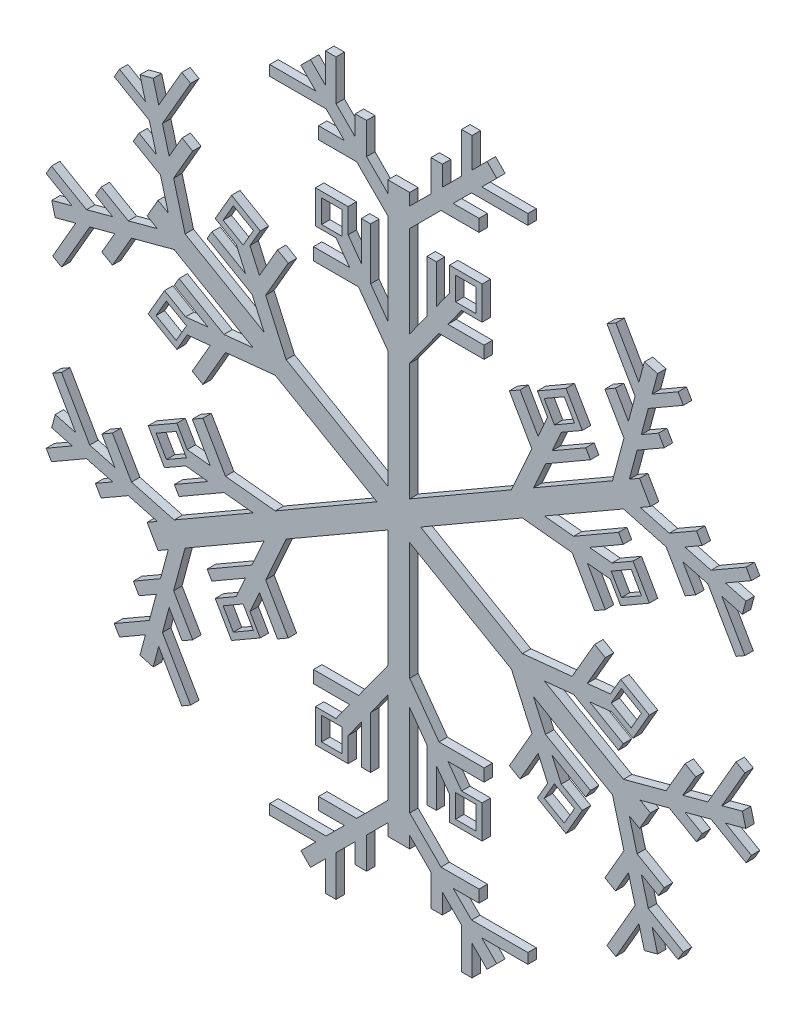
SolidWorks part; units mm, degrees
ref_plane "Front Plane" through (0, 0, 0) normal (0, 0, 1) x (1, 0, 0)
ref_plane "Top Plane" through (0, 0, 0) normal (0, 1, 0) x (1, 0, 0)
ref_plane "Right Plane" through (0, 0, 0) normal (1, 0, 0) x (0, 0, -1)
sketch "Sketch3" plane through (0, 0, 0) normal (0, 0, 1) x (1, 0, 0)
  line L0 (-3.2918, 12.5643) -> (-12.115, 24.7697)
  line L2 (-3.2918, -25.3618) -> (-3.2918, 12.5643)
  line L3 (-3.2918, 57.1281) -> (0, 57.1281)
  line L4 (0, -28.3059) -> (0, 57.1281)
  line L6 (-15.2752, 36.8018) -> (-11.2955, 31.2966)
  line L7 (-11.2955, 31.2966) -> (-11.2955, 43.0417)
  line L8 (-11.2955, 43.0417) -> (-8.4779, 43.0417)
  line L9 (-8.4779, 43.0417) -> (-8.4779, 27.3989)
  line L10 (-9.7069, 59.976) -> (-9.7069, 69.4227)
  line L11 (-12.115, 24.7697) -> (-25.6946, 24.7697)
  line L12 (-25.6946, 24.7697) -> (-25.6946, 28.4918)
  line L13 (-25.6946, 28.4918) -> (-14.8057, 28.4918)
  line L14 (-3.2918, 20.2248) -> (-3.2918, 47.7181)
  line L15 (-8.4779, 27.3989) -> (-3.2918, 20.2248)
  line L16 (-14.8057, 28.4918) -> (-18.9123, 34.1725)
  line L17 (-3.2918, 47.7181) -> (-12.7019, 57.1281)
  line L18 (-29.5153, 73.9416) -> (-26.5939, 76.863)
  line L19 (-26.5939, 76.863) -> (-22.075, 72.3441)
  line L20 (-9.7069, 69.4227) -> (-13.1345, 69.4227)
  line L21 (-21.9078, 66.3341) -> (-38.8829, 66.3341)
  line L22 (-13.1345, 69.4227) -> (-13.1345, 63.4036)
  line L23 (-24.9964, 69.4227) -> (-29.5153, 73.9416)
  line L24 (-16.388, 60.8143) -> (-24.1695, 60.8143)
  line L25 (-24.1695, 60.8143) -> (-24.1695, 57.1281)
  line L26 (-24.1695, 57.1281) -> (-12.7019, 57.1281)
  line L27 (-38.8829, 66.3341) -> (-38.8829, 69.4227)
  line L28 (-16.388, 60.8143) -> (-21.9078, 66.3341)
  line L29 (-38.8829, 69.4227) -> (-24.9964, 69.4227)
  line L30 (-18.9123, 69.1813) -> (-13.1345, 63.4036)
  line L31 (-22.075, 72.3441) -> (-22.075, 81.3818)
  line L32 (-22.075, 81.3818) -> (-18.9123, 81.3818)
  line L33 (-18.9123, 81.3818) -> (-18.9123, 69.1813)
  line L34 (-25.111, 44.1521) -> (-15.2752, 44.1521)
  line L35 (-25.111, 44.1521) -> (-25.111, 34.1725)
  line L36 (-25.111, 34.1725) -> (-18.9123, 34.1725)
  line L37 (-15.2752, 44.1521) -> (-15.2752, 36.8018)
  line L42 (-23.2593, 42.4548) -> (-17.0937, 42.4548)
  line L47 (-23.2593, 42.4548) -> (-23.2593, 35.4871)
  line L48 (-23.2593, 35.4871) -> (-17.0937, 35.4871)
  line L49 (-17.0937, 42.4548) -> (-17.0937, 35.4871)
  line L50 (-9.7069, 59.976) -> (-3.2918, 53.5609)
  line L51 (-3.2918, 53.5609) -> (-3.2918, 57.1281)
  arc A1 (-3.2918, -25.3618) -> (-0.0449, -28.3104) centre (-0.3295, -25.3618) ccw
  arc A2 (-0.0449, -28.3104) -> (0, -28.3059) centre (0, -28.5278) ccw
  point P37 (-3.3229, -15.2408)
  point P47 (-3.2918, -25.3618)
extrude "Boss-Extrude2" add sketch "Sketch3" along normal blind 2.54
pattern_circular "CirPattern3" count 6 over 360 about axis through (0, -28.5278, 0) along (0, 0, 1) of "Boss-Extrude2"
mirror "Mirror2" about plane through (0, -28.3059, 2.54) normal (-1, 0, 0) of "Boss-Extrude2"
mirror "Mirror4" about plane through (-0.1922, -28.4168, 2.54) normal (-0.5, -0.866, 0) of "CirPattern3", "Boss-Extrude2"
